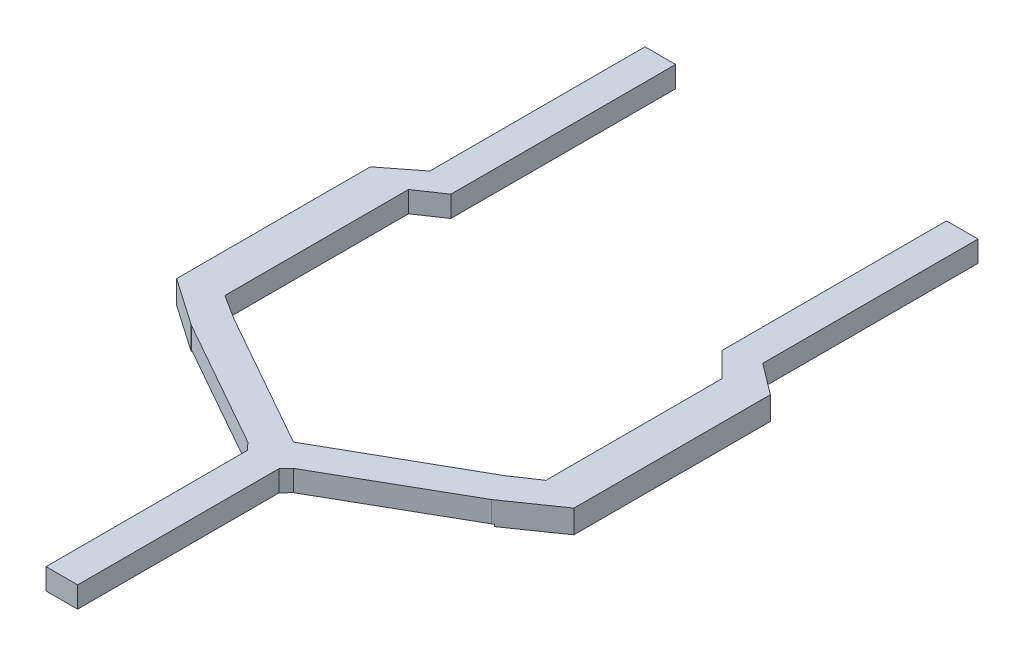
SolidWorks part; units mm, degrees
ref_plane "Front Plane" through (0, 0, 0) normal (0, 0, 1) x (1, 0, 0)
ref_plane "Top Plane" through (0, 0, 0) normal (0, 1, 0) x (1, 0, 0)
ref_plane "Right Plane" through (0, 0, 0) normal (1, 0, 0) x (0, 0, -1)
sketch "Sketch2" plane through (0, 0, 0) normal (0, 1, 0) x (1, 0, 0)
  line L0 (0, 0) -> (0, 90.3579)
  line L1 (0, 90.3579) -> (20.066, 90.3579)
  line L2 (0, 90.3579) -> (-20.066, 90.3579)
  line L3 (0, 90.3579) -> (0, 27.9178)
  line L4 (-20.066, 90.3579) -> (-20.066, 37.1524)
  line L5 (20.066, 90.3579) -> (20.066, 37.1524)
  line L6 (-16.3804, 37.1524) -> (0, 27.9178)
  line L7 (-20.066, 90.3579) -> (-16.3804, 90.3579)
  line L8 (-20.066, 90.3579) -> (-20.066, 37.1524)
  line L9 (-20.066, 37.1524) -> (-16.3804, 37.1524)
  line L10 (-16.3804, 90.3579) -> (-16.3804, 37.1524)
  line L11 (20.066, 90.3579) -> (16.2705, 90.3579)
  line L12 (20.066, 90.3579) -> (20.066, 37.1524)
  line L13 (20.066, 37.1524) -> (16.2705, 37.1524)
  line L14 (16.2705, 90.3579) -> (16.2705, 37.1524)
  line L15 (16.2705, 37.1524) -> (0, 27.9178)
  line L16 (0, 0) -> (1.905, 0)
  line L17 (0, 0) -> (-1.905, 0)
  line L18 (16.2705, 37.1524) -> (18.1394, 33.9643)
  line L19 (-16.3804, 37.1524) -> (-18.3592, 33.9643)
  line L20 (0, 25.1694) -> (-1.905, 25.1694)
  line L21 (1.905, 0) -> (1.905, 24.29)
  line L22 (20.066, 37.1524) -> (18.1394, 33.9643)
  line L23 (18.1394, 33.9643) -> (2.7484, 25.1694)
  line L24 (0, 25.1694) -> (1.905, 25.1694)
  line L25 (1.905, 24.29) -> (2.7484, 25.1694)
  line L26 (-20.066, 37.1524) -> (-18.3592, 33.9643)
  line L27 (-1.905, 0) -> (-1.905, 24.29)
  line L28 (-18.3592, 33.9643) -> (-2.7484, 25.1694)
  line L29 (-2.7484, 25.1694) -> (-1.905, 24.29)
extrude "Boss-Extrude1" add sketch "Sketch2" along normal blind 2.54
sketch "Sketch3" plane through (0, 2.54, 0) normal (0, 1, 0) x (1, 0, 0)
  line L0 (-23.8437, 64.4164) -> (24.1982, 64.4164)
  line L1 (-16.3804, 90.3579) -> (-16.3804, 37.1524) construction
  line L2 (-16.3804, 64.4164) -> (-24.0938, 64.4164)
  line L3 (-16.3804, 64.4164) -> (-16.3804, 34.013)
  line L4 (-16.3804, 34.013) -> (-24.0938, 34.013)
  line L5 (-24.0938, 64.4164) -> (-24.0938, 34.013)
  line M20 (-20.066, 90.3579) -> (-20.066, 37.1524)
  line M21 (-20.066, 37.1524) -> (-18.3592, 33.9643)
extrude "Boss-Extrude3" add sketch "Sketch3" against normal blind 2.794 contours L2 L5 L4 L0 M21 M20
sketch "Sketch5" plane through (0, 2.54, 0) normal (0, 1, 0) x (1, 0, 0)
  line L0 (-20.066, 64.4164) -> (25.1171, 64.4164)
  line L1 (16.2705, 90.3579) -> (16.2705, 37.1524) construction
  line L2 (16.2705, 64.4164) -> (23.7979, 64.4164)
  line L3 (16.2705, 64.4164) -> (16.2705, 33.8544)
  line L4 (16.2705, 33.8544) -> (23.7979, 33.8544)
  line L5 (23.7979, 64.4164) -> (23.7979, 33.8544)
  line M7 (2.7484, 25.1694) -> (18.1394, 33.9643)
  line M8 (18.1394, 33.9643) -> (20.066, 37.1524)
  line M9 (20.066, 37.1524) -> (20.066, 90.3579)
extrude "Boss-Extrude4" add sketch "Sketch5" against normal blind 2.794 contours L5 L0 L4 M9 M8 M7
sketch "Sketch6" plane through (0, 2.54, 0) normal (0, 1, 0) x (1, 0, 0)
  line L0 (-16.3804, 37.1524) -> (-19.4253, 39.0792)
  line L1 (-19.4253, 39.0792) -> (-19.4253, 61.2163)
  line L2 (-19.4253, 61.2163) -> (-16.3804, 63.2741)
  line L3 (-16.3804, 90.3579) -> (-16.3804, 37.1524) construction
  line L4 (-16.3804, 63.2741) -> (-16.3804, 37.1524)
extrude "Cut-Extrude1" cut sketch "Sketch6" against normal blind 2.794
sketch "Sketch7" plane through (0, 2.54, 0) normal (0, 1, 0) x (1, 0, 0)
  line L0 (16.2705, 37.1524) -> (19.2108, 39.1313)
  line L1 (19.2108, 39.1313) -> (19.2108, 60.3488)
  line L2 (19.2108, 60.3488) -> (16.0226, 63.5369)
  line L3 (16.0226, 63.5369) -> (16.2705, 37.1524)
extrude "Cut-Extrude2" cut sketch "Sketch7" against normal blind 2.794
sketch "Sketch8" plane through (0, 2.54, 0) normal (0, 1, 0) x (1, 0, 0)
  line L0 (-18.3592, 33.9643) -> (-25.9828, 39.2412)
  line L1 (-25.9828, 39.2412) -> (-25.9828, 59.7991)
  line L2 (-25.9828, 59.7991) -> (-20.066, 64.4164)
  line L3 (-20.066, 64.4164) -> (-26.7041, 65.2353)
  line L4 (-26.7041, 65.2353) -> (-32.1392, 50.7844)
  line L5 (-32.1392, 50.7844) -> (-24.0938, 30.8861)
  line L6 (-24.0938, 30.8861) -> (-18.3592, 33.9643)
extrude "Cut-Extrude3" cut sketch "Sketch8" against normal blind 2.794
sketch "Sketch9" plane through (0, 2.54, 0) normal (0, 1, 0) x (1, 0, 0)
  line L0 (17.947, 33.8544) -> (23.7979, 37.922)
  line L1 (23.7979, 64.4164) -> (23.7979, 33.8544) construction
  line L2 (23.7979, 37.922) -> (26.5357, 53.1492)
  line L3 (26.5357, 53.1492) -> (25.1668, 60.5687)
  line L4 (25.1668, 60.5687) -> (20.066, 64.4164)
  line L5 (20.066, 64.4164) -> (22.6164, 67.7974)
  line L6 (22.6164, 67.7974) -> (32.0632, 64.4164)
  line L7 (32.0632, 64.4164) -> (29.0949, 33.8544)
  line L8 (29.0949, 33.8544) -> (20.4412, 27.8383)
  line L9 (20.4412, 27.8383) -> (17.947, 33.8544)
extrude "Cut-Extrude4" cut sketch "Sketch9" against normal blind 2.794
